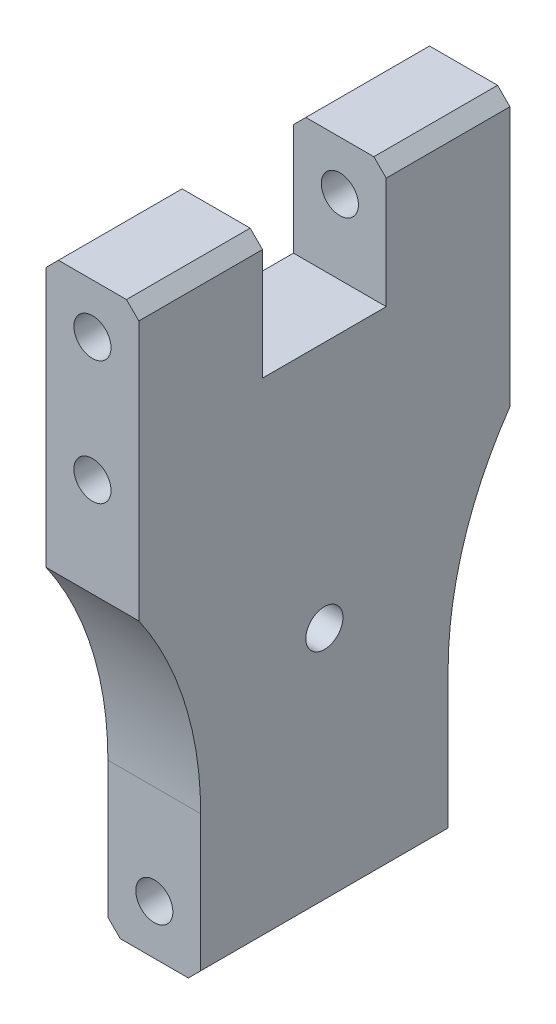
SolidWorks part; units mm, degrees
ref_plane "Front Plane" through (0, 0, 0) normal (0, 0, 1) x (1, 0, 0)
ref_plane "Top Plane" through (0, 0, 0) normal (0, 1, 0) x (1, 0, 0)
ref_plane "Right Plane" through (0, 0, 0) normal (1, 0, 0) x (0, 0, -1)
sketch "Sketch1" plane through (0, 0, 0) normal (1, 0, 0) x (0, 0, -1)
  line L0 (25.4, 101.6) -> (25.4, 0) construction
  line L1 (50.8, 0) -> (50.8, 30.48)
  line L2 (-12.7, 127) -> (12.7, 127)
  line L3 (12.7, 127) -> (12.7, 101.6)
  line L4 (12.7, 101.6) -> (38.1, 101.6)
  line L5 (63.5, 127) -> (63.5, 71.12)
  line L6 (-12.7, 127) -> (-12.7, 71.12)
  line L7 (0, 0) -> (0, 30.48)
  line L8 (38.1, 127) -> (38.1, 101.6)
  line L9 (63.5, 127) -> (38.1, 127)
  line L11 (50.8, 0) -> (0, 0)
  arc A0 (-12.7, 71.12) -> (0, 30.48) centre (-71.374, 30.48) cw
  arc A1 (63.5, 71.12) -> (50.8, 30.48) centre (122.174, 30.48) ccw
  dimension "D1" = 50.8
  dimension "D2" = 76.2
  dimension "D3" = 25.4
  dimension "D4" = 101.6
  dimension "D5" = 30.48
  dimension "D6" = 55.88
  dimension "D7" = 25.4
extrude "Boss-Extrude1" add sketch "Sketch1" along normal blind 19.05
sketch "Sketch2" plane through (0, 0, 12.7) normal (0, 0, 1) x (1, 0, 0)
  line L0 (19.05, 127) -> (0, 127) construction
  line L1 (9.525, 127) -> (9.525, 116.84) construction
  line L2 (9.525, 116.84) -> (9.525, 91.44) construction
  line L3 (19.05, 0) -> (0, 0) construction
  circle A0 centre (9.525, 116.84) radius 3.81
  circle A1 centre (9.525, 91.44) radius 3.81
  circle A2 centre (9.525, 10.16) radius 3.81
  dimension "D1" = 10.16
  dimension "D2" = 10.16
  dimension "D3" = 10.16
extrude "Cut-Extrude1" cut sketch "Sketch2" against normal through all
sketch "Sketch3" plane through (19.05, 0, 0) normal (1, 0, 0) x (0, 0, -1)
  line L0 (25.4, 50.8) -> (25.4, 101.6) construction
  line L1 (38.1, 101.6) -> (12.7, 101.6) construction
  circle A0 centre (25.4, 50.8) radius 3.81
  dimension "D1" = 50.8
extrude "Cut-Extrude2" cut sketch "Sketch3" against normal through all
chamfer "Chamfer1" distance 2.54 angle 45 6 edges at (0, 0, -25.4) (19.05, 0, -25.4) (0, 127, 0) (0, 127, -50.8) (19.05, 127, -50.8) (19.05, 127, 0)
